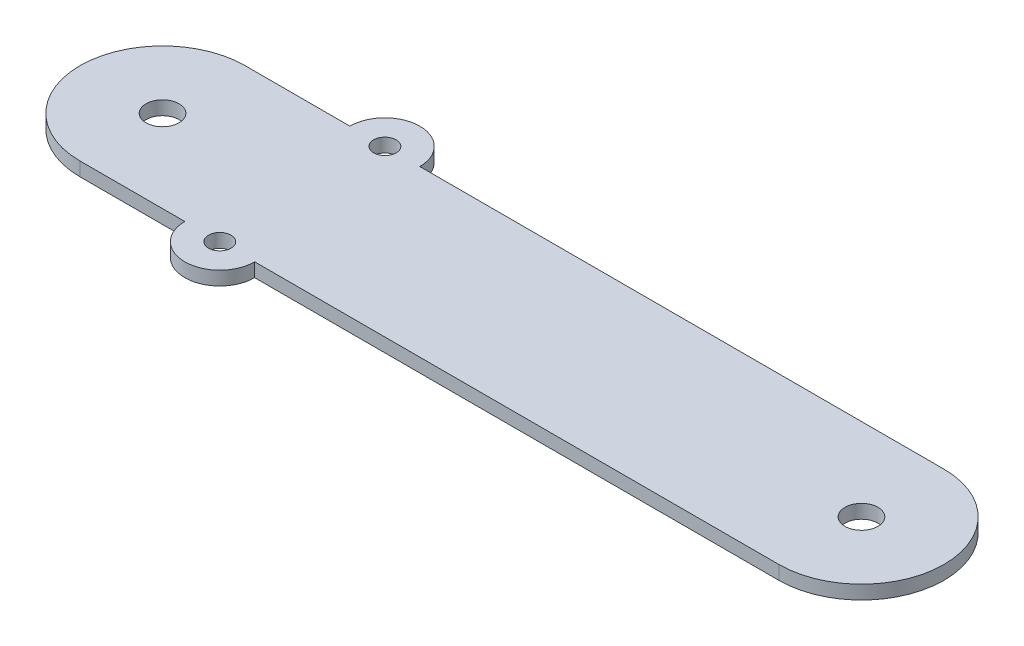
SolidWorks part; units mm, degrees
ref_plane "Front Plane" through (0, 0, 0) normal (0, 0, 1) x (1, 0, 0)
ref_plane "Top Plane" through (0, 0, 0) normal (0, 1, 0) x (1, 0, 0)
ref_plane "Right Plane" through (0, 0, 0) normal (1, 0, 0) x (0, 0, -1)
sketch "Sketch1" plane through (0, 0, 0) normal (0, 1, 0) x (1, 0, 0)
  line L0 (-127, 0) -> (127, 0) construction
  line L1 (-127, 30) -> (127, 30)
  line L2 (-127, -30) -> (127, -30)
  arc A0 (-127, 30) -> (-127, -30) centre (-127, 0) ccw
  arc A1 (127, -30) -> (127, 30) centre (127, 0) ccw
  arc A2 (-88.9, 30) -> (-63.5, 30) centre (-76.2, 30) cw
  arc A3 (-88.9, -30) -> (-63.5, -30) centre (-76.2, -30) ccw
  point P2 (0, 0)
  point P11 (0, 0)
  dimension "D3" = 12.7
  dimension "D1" = 254
  dimension "D2" = 60
  dimension "D4" = 38.1
extrude "Boss-Extrude1" add sketch "Sketch1" along normal mid plane 5
hole_wizard "Ø12.0mm Dowel Hole1" positions "Sketch2" profile "Sketch3" hole size "Ø12.0" standard "ANSI Metric" end condition up to next
sketch "Sketch2" plane through (0, 2.5, 0) normal (0, 1, 0) x (1, 0, 0)
  point P0 (-127, 0)
  point P2 (127, 0)
  point P4 (-100.9166, 2.437)
  point P6 (104.3697, 9.2428)
sketch "Sketch3" plane through (-127, 2.5, 0) normal (1, 0, 0) x (0, 0, 1)
  line L0 (0, 0) -> (0, 5)
  line L1 (0, 5) -> (6, 5)
  line L2 (6, 5) -> (6, 0)
  line L5 (6, 0) -> (0, 0)
  line L11 (0, -6.35) -> (0, 107.95) construction
  dimension "Thru Hole Dia." = 12
  dimension "Thru Hole Depth" = 5
hole_wizard "Ø8.0mm Dowel Hole1" positions "Sketch4" profile "Sketch5" hole size "Ø8.0" standard "ANSI Metric" end condition up to next
sketch "Sketch4" plane through (0, 2.5, 0) normal (0, 1, 0) x (1, 0, 0)
  arc A0 (-63.5, 30) -> (-88.9, 30) centre (-76.2, 30) ccw construction
  arc A1 (-88.9, -30) -> (-63.5, -30) centre (-76.2, -30) ccw construction
  point P0 (-76.2, 30)
  point P2 (-76.2, -30)
  point P4 (-70.1729, 26.0998)
  point P5 (0, 0)
  point P9 (0, 0)
sketch "Sketch5" plane through (-76.2, 2.5, -30) normal (1, 0, 0) x (0, 0, 1)
  line L0 (0, 0) -> (0, 5)
  line L1 (0, 5) -> (4.1, 5)
  line L2 (4.1, 5) -> (4.1, 0)
  line L5 (4.1, 0) -> (0, 0)
  line L11 (0, -6.35) -> (0, 107.95) construction
  dimension "Thru Hole Dia." = 8.2
  dimension "Thru Hole Depth" = 5
